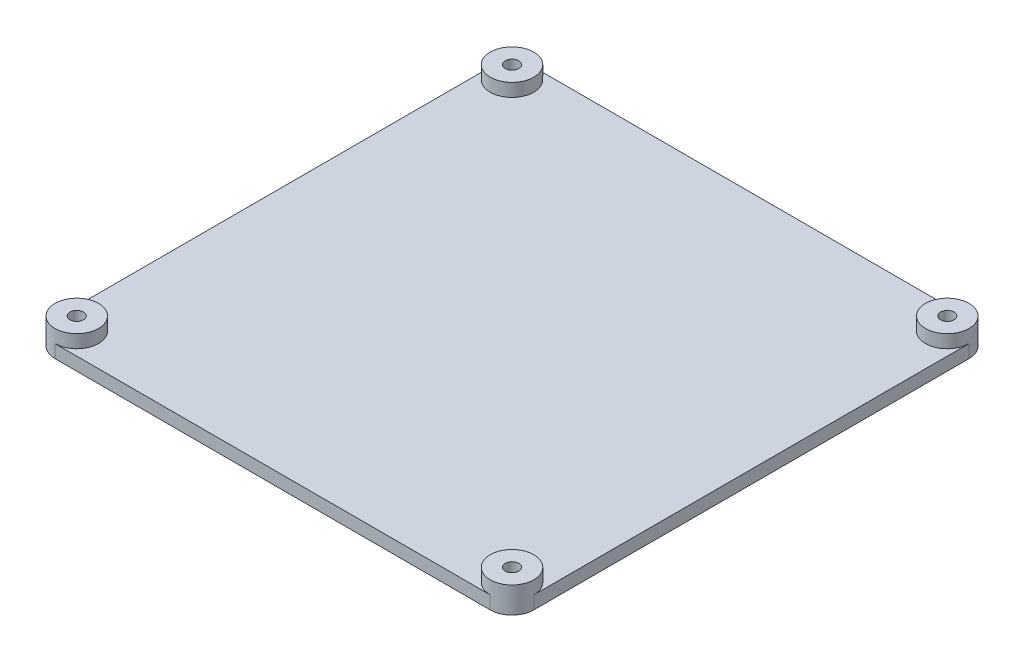
SolidWorks part; units mm, degrees
ref_plane "Front Plane" through (0, 0, 0) normal (0, 0, 1) x (1, 0, 0)
ref_plane "Top Plane" through (0, 0, 0) normal (0, 1, 0) x (1, 0, 0)
ref_plane "Right Plane" through (0, 0, 0) normal (1, 0, 0) x (0, 0, -1)
sketch "Sketch1" plane through (0, 0, 0) normal (0, 1, 0) x (1, 0, 0)
  line L1 (-55, 55) -> (55, 55)
  line L2 (-55, 55) -> (-55, -55)
  line L3 (-55, -55) -> (55, -55)
  line L4 (55, 55) -> (55, -55)
  point P0 (0, 0)
  dimension "D1" = 110
  dimension "D2" = 110
extrude "Boss-Extrude1" add sketch "Sketch1" along normal blind 3
fillet "Fillet1" radius 5 4 edges at (-55, 1.5, -55) (55, 1.5, -55) (55, 1.5, 55) (-55, 1.5, 55)
sketch "Sketch2" plane through (0, 3, 0) normal (0, 1, 0) x (1, 0, 0)
  circle A0 centre (-50, 50) radius 5
  circle A1 centre (50, 50) radius 5
  circle A2 centre (50, -50) radius 5
  circle A3 centre (-50, -50) radius 5
extrude "Boss-Extrude2" add sketch "Sketch2" along normal blind 3
sketch "Sketch6" plane through (0, 0, 0) normal (0, -1, 0) x (1, 0, 0)
  circle A0 centre (-50, 50) radius 1.55
  circle A1 centre (50, -50) radius 1.55
  circle A2 centre (50, 50) radius 1.55
  circle A3 centre (-50, -50) radius 1.55
  dimension "D1" = 3.1
  dimension "D2" = 3.1
  dimension "D3" = 3.1
  dimension "D4" = 3.1
extrude "Cut-Extrude1" cut sketch "Sketch6" against normal through all
